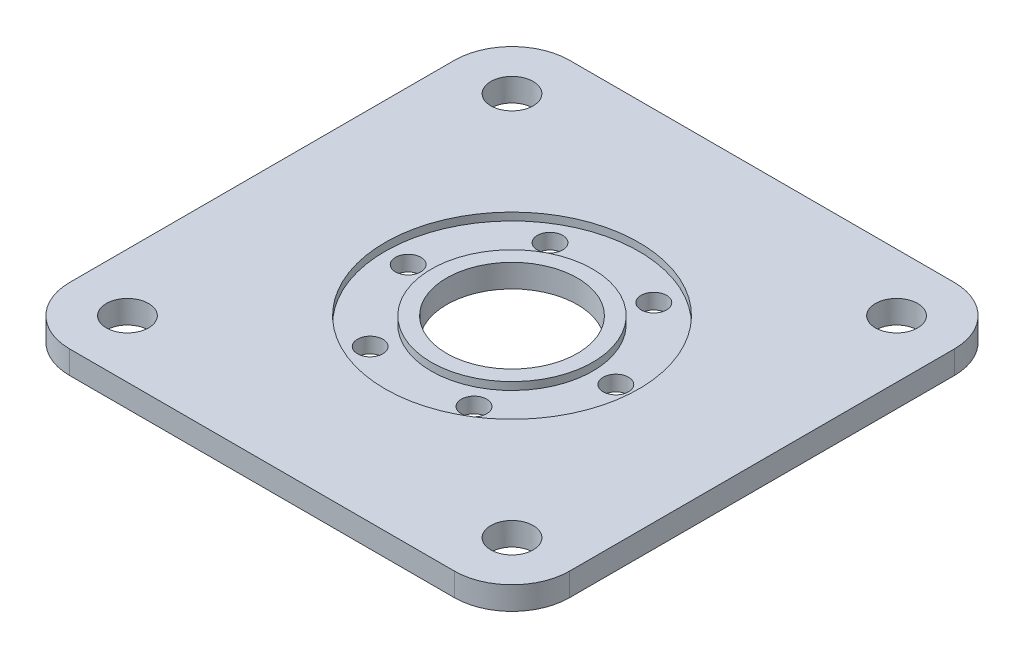
SolidWorks part; units mm, degrees
ref_plane "Front Plane" through (0, 0, 0) normal (0, 0, 1) x (1, 0, 0)
ref_plane "Top Plane" through (0, 0, 0) normal (0, 1, 0) x (1, 0, 0)
ref_plane "Right Plane" through (0, 0, 0) normal (1, 0, 0) x (0, 0, -1)
sketch "Sketch1" plane through (0, 0, 0) normal (0, 1, 0) x (1, 0, 0)
  line L1 (-50, -65) -> (50, -65)
  line L2 (-65, -50) -> (-65, 50)
  line L3 (-50, 65) -> (50, 65)
  line L4 (65, -50) -> (65, 50)
  line L5 (-65, -65) -> (65, 65) construction
  line L6 (-65, 65) -> (65, -65) construction
  arc A0 (-50, -65) -> (-65, -50) centre (-50, -50) cw
  arc A1 (-65, 50) -> (-50, 65) centre (-50, 50) cw
  arc A2 (65, 50) -> (50, 65) centre (50, 50) ccw
  arc A3 (50, -65) -> (65, -50) centre (50, -50) ccw
  circle A4 centre (0, 0) radius 17
  point P0 (0, 0)
  dimension "D1" = 15
  dimension "D2" = 34
  dimension "D3" = 130
extrude "Boss-Extrude1" add sketch "Sketch1" along normal blind 6
sketch "Sketch2" plane through (0, 6, 0) normal (0, 1, 0) x (1, 0, 0)
  circle A0 centre (0, 0) radius 21
  circle A1 centre (0, 0) radius 33
  dimension "D1" = 42
  dimension "D2" = 12
extrude "Cut-Extrude1" cut sketch "Sketch2" against normal blind 2
sketch "Sketch3" plane through (0, 6, 0) normal (0, 1, 0) x (1, 0, 0)
  line L1 (-50, -50) -> (50, -50) construction
  line L2 (-50, -50) -> (-50, 50) construction
  line L3 (-50, 50) -> (50, 50) construction
  line L4 (50, -50) -> (50, 50) construction
  line L5 (-50, -50) -> (50, 50) construction
  line L6 (-50, 50) -> (50, -50) construction
  circle A0 centre (-50, 50) radius 5.5
  circle A1 centre (50, 50) radius 5.5
  circle A2 centre (50, -50) radius 5.5
  circle A3 centre (-50, -50) radius 5.5
  point P0 (0, 0)
  dimension "D2" = 11
  dimension "D1" = 100
extrude "Cut-Extrude2" cut sketch "Sketch3" against normal through all both and the other way through all
sketch "Sketch4" plane through (0, 4, 0) normal (0, 1, 0) x (1, 0, 0)
  point P0 (-27, 0)
  dimension "D1" = 27
hole_wizard "M6 Clearance Hole1" positions "3DSketch1" profile "Sketch5" hole size "M6" standard "ISO" end condition up to next
sketch3d "3DSketch1"
  point P0 (-27, 4, 0)
sketch "Sketch5" plane through (-27, 4, 0) normal (1, 0, 0) x (0, 0, 1)
  line L0 (0, 0) -> (0, 4)
  line L1 (0, 4) -> (3.3, 4)
  line L2 (3.3, 4) -> (3.3, 0)
  line L5 (3.3, 0) -> (0, 0)
  line L11 (0, -6.35) -> (0, 107.95) construction
  dimension "Thru Hole Dia." = 6.6
  dimension "Thru Hole Depth" = 4
pattern_circular "CirPattern1" count 6 over 360 about axis through (0, 0, 0) along (0, 1, 0) of "M6 Clearance Hole1"
sketch "Sketch6" [suppressed] plane through (0, 6, 0) normal (0, 1, 0) x (1, 0, 0)
  line L5 (-33, 48) -> (-33, -18) construction
  line L6 (-33, -18) -> (33, -18) construction
  line L7 (33, -18) -> (33, 48) construction
  line L8 (33, 48) -> (-33, 48) construction
  line L9 (0, 0) -> (0, 15) construction
  line L10 (33, 15) -> (-33, 15) construction
  circle A5 centre (33, -18) radius 2.5
  circle A6 centre (33, 48) radius 2.5
  circle A7 centre (-33, 48) radius 2.5
  circle A8 centre (-33, -18) radius 2.5
  dimension "D3" = 5
  dimension "D1" = 66
  dimension "D2" = 15
